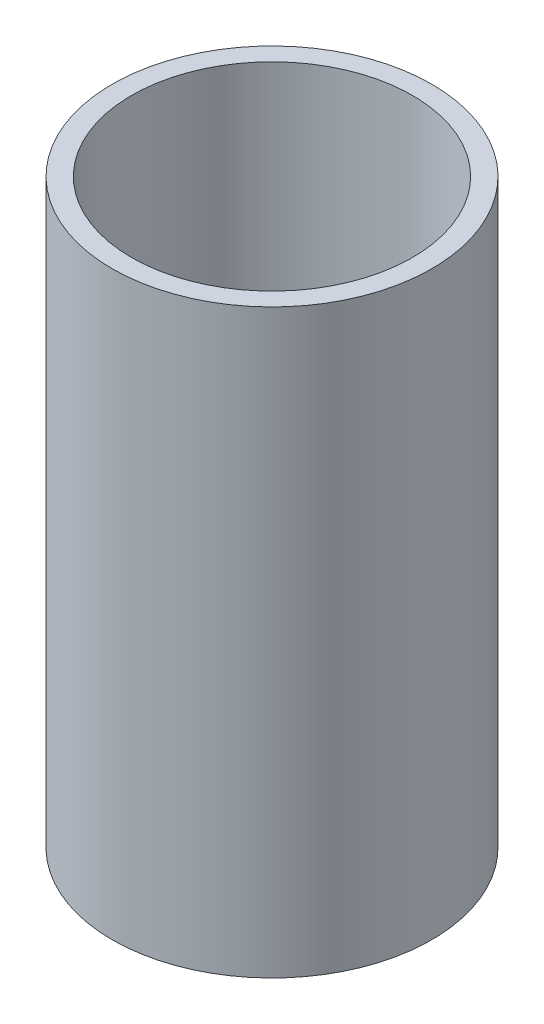
SolidWorks part; units mm, degrees
ref_plane "Front Plane" through (0, 0, 0) normal (0, 0, 1) x (1, 0, 0)
ref_plane "Top Plane" through (0, 0, 0) normal (0, 1, 0) x (1, 0, 0)
ref_plane "Right Plane" through (0, 0, 0) normal (1, 0, 0) x (0, 0, -1)
sketch "Sketch1" plane through (0, 0, 0) normal (0, 1, 0) x (1, 0, 0)
  circle A0 centre (0, 0) radius 33
  circle A1 centre (0, 0) radius 29
  dimension "D1" = 66
  dimension "D3" = 58
  dimension "D2" = 4
extrude "Boss-Extrude1" add sketch "Sketch1" along normal blind 120
